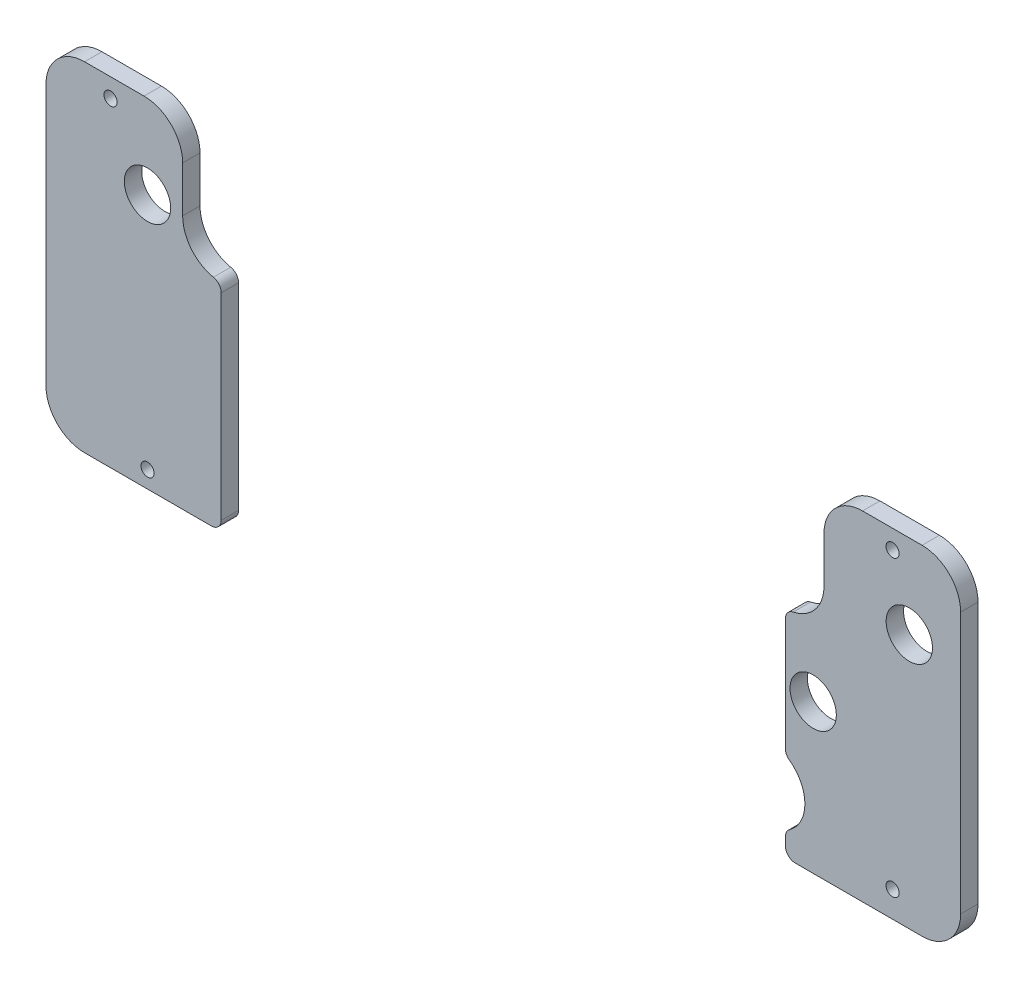
SolidWorks part; units mm, degrees
ref_plane "Front Plane" through (0, 0, 0) normal (0, 0, 1) x (1, 0, 0)
ref_plane "Top Plane" through (0, 0, 0) normal (0, 1, 0) x (1, 0, 0)
ref_plane "Right Plane" through (0, 0, 0) normal (1, 0, 0) x (0, 0, -1)
sketch "Sketch1" plane through (0, 0, 0) normal (0, 0, 1) x (1, 0, 0)
  line L8 (83.2228, -305.8774) -> (83.2228, -335.0874)
  line L9 (-62.9682, -305.8774) -> (-62.9682, -356.9247)
  line L10 (85.7628, -359.4647) -> (118.6273, -359.4647)
  line L11 (83.2228, -354.7836) -> (83.2228, -356.9247)
  line L16 (-108.3727, -281.7188) -> (-108.3727, -349.4647)
  line L17 (-98.3727, -359.4647) -> (-65.5082, -359.4647)
  line L18 (128.6273, -349.4647) -> (128.6273, -281.7188)
  line L19 (118.6273, -271.7188) -> (103.2228, -271.7188)
  line L20 (93.2228, -281.7188) -> (93.2228, -293.5973)
  line L22 (-72.9682, -293.5973) -> (-72.9682, -281.7188)
  line L23 (-82.9682, -271.7188) -> (-98.3727, -271.7188)
  arc A8 (84.2798, -352.7214) -> (84.2798, -337.1496) centre (78.681, -344.9355) ccw
  arc A9 (-62.9682, -305.8774) -> (-64.9937, -303.39) centre (-65.5082, -305.8774) ccw
  arc A10 (-65.5082, -359.4647) -> (-62.9682, -356.9247) centre (-65.5082, -356.9247) ccw
  arc A11 (85.2483, -303.39) -> (83.2228, -305.8774) centre (85.7628, -305.8774) ccw
  arc A12 (84.2798, -337.1496) -> (83.2228, -335.0874) centre (85.7628, -335.0874) cw
  arc A13 (84.2798, -352.7214) -> (83.2228, -354.7836) centre (85.7628, -354.7836) ccw
  arc A14 (83.2228, -356.9247) -> (85.7628, -359.4647) centre (85.7628, -356.9247) ccw
  arc A16 (-108.3727, -349.4647) -> (-98.3727, -359.4647) centre (-98.3727, -349.4647) ccw
  arc A17 (118.6273, -359.4647) -> (128.6273, -349.4647) centre (118.6273, -349.4647) ccw
  arc A18 (128.6273, -281.7188) -> (118.6273, -271.7188) centre (118.6273, -281.7188) ccw
  arc A19 (103.2228, -271.7188) -> (93.2228, -281.7188) centre (103.2228, -281.7188) ccw
  arc A20 (85.2483, -303.39) -> (93.2228, -293.5973) centre (83.2228, -293.5973) ccw
  arc A21 (-72.9682, -293.5973) -> (-64.9937, -303.39) centre (-62.9682, -293.5973) ccw
  arc A22 (-72.9682, -281.7188) -> (-82.9682, -271.7188) centre (-82.9682, -281.7188) ccw
  arc A23 (-98.3727, -271.7188) -> (-108.3727, -281.7188) centre (-98.3727, -281.7188) ccw
  point P39 (83.2228, -353.3818)
  point P42 (83.2228, -359.4647)
  dimension "D1" = 2.54
extrude "Boss-Extrude1" add sketch "Sketch1" along normal blind 4.5
hole_wizard "M3 Clearance Hole1" positions "Sketch3" profile "Sketch2" hole size "M3" standard "ISO" end condition through all
sketch "Sketch3" plane through (0, 0, 4.5) normal (0, 0, 1) x (1, 0, 0)
  point P0 (115.3273, -293.4157)
  point P2 (-82.0727, -293.4157)
  point P4 (90.4173, -320.9157)
  point P7 (-82.0727, -355.0776)
sketch "Sketch2" plane through (115.3273, -293.4157, 4.5) normal (1, 0, 0) x (0, -1, 0)
  line L0 (0, 0) -> (0, 4.5)
  line L1 (0, 4.5) -> (1.7, 4.5)
  line L2 (1.7, 4.5) -> (1.7, 0)
  line L5 (1.7, 0) -> (0, 0)
  line L11 (0, -6.35) -> (0, 107.95) construction
  dimension "Thru Hole Dia." = 3.4
  dimension "Thru Hole Depth" = 4.5
sketch "Sketch4" plane through (0, 0, 4.5) normal (0, 0, 1) x (1, 0, 0)
  circle A0 centre (115.3273, -293.4157) radius 6
  circle A1 centre (90.4173, -320.9157) radius 6
  circle A2 centre (-82.0727, -293.4157) radius 6
  dimension "D1" = 12
  dimension "D2" = 12
  dimension "D3" = 12
extrude "Cut-Extrude1" cut sketch "Sketch4" against normal blind 10
hole_wizard "M3 Clearance Hole2" positions "Sketch6" profile "Sketch5" hole size "M3" standard "ISO" end condition through all
sketch "Sketch6" plane through (0, 0, 4.5) normal (0, 0, 1) x (1, 0, 0)
  point P0 (110.9921, -276.5975)
  point P2 (110.9921, -352.7227)
  point P4 (-91.6539, -276.5975)
sketch "Sketch5" plane through (110.9921, -276.5975, 4.5) normal (1, 0, 0) x (0, -1, 0)
  line L0 (0, 0) -> (0, 4.5)
  line L1 (0, 4.5) -> (1.7, 4.5)
  line L2 (1.7, 4.5) -> (1.7, 0)
  line L5 (1.7, 0) -> (0, 0)
  line L11 (0, -6.35) -> (0, 107.95) construction
  dimension "Thru Hole Dia." = 3.4
  dimension "Thru Hole Depth" = 4.5
